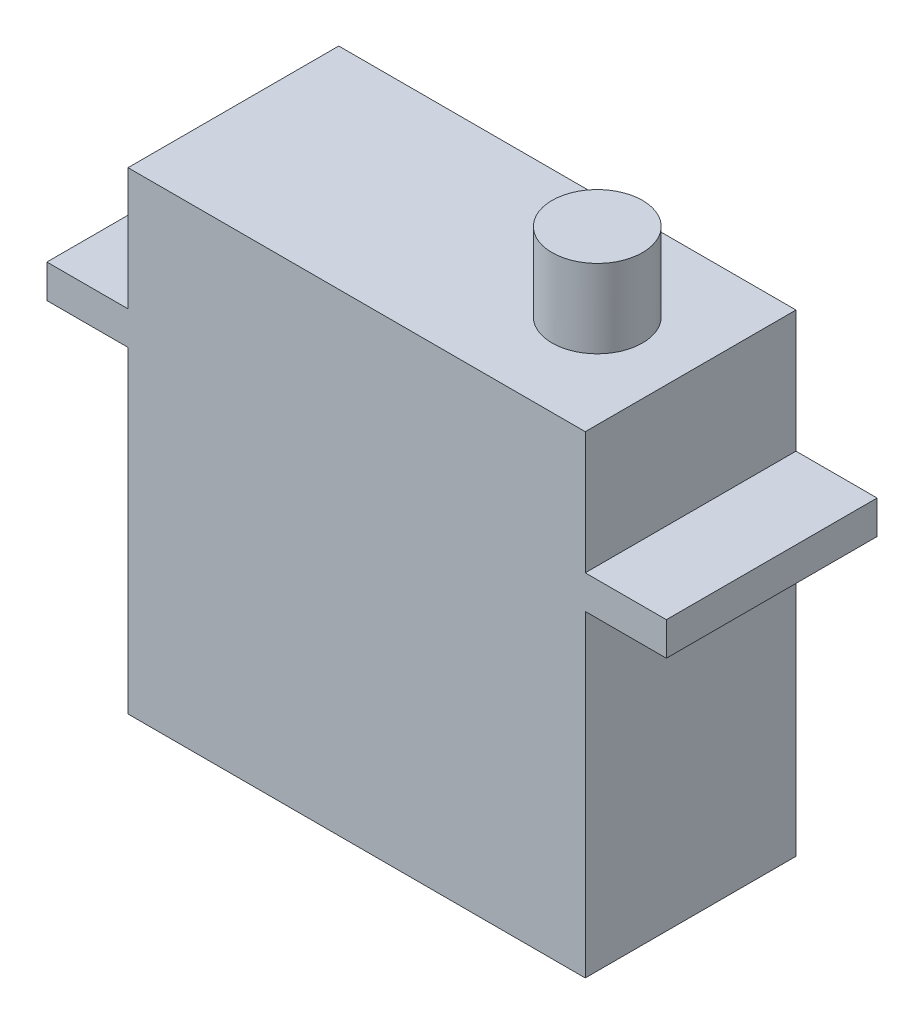
SolidWorks part; units mm, degrees
ref_plane "Front Plane" through (0, 0, 0) normal (0, 0, 1) x (1, 0, 0)
ref_plane "Top Plane" through (0, 0, 0) normal (0, 1, 0) x (1, 0, 0)
ref_plane "Right Plane" through (0, 0, 0) normal (1, 0, 0) x (0, 0, -1)
sketch "Sketch1" plane through (0, 0, 0) normal (0, 0, 1) x (1, 0, 0)
  line L1 (-14.605, 15.113) -> (14.605, 15.113)
  line L2 (-14.605, 15.113) -> (-14.605, -15.113)
  line L3 (-14.605, -15.113) -> (14.605, -15.113)
  line L4 (14.605, 15.113) -> (14.605, -15.113)
  line L5 (-14.605, 15.113) -> (14.605, -15.113) construction
  line L6 (-14.605, -15.113) -> (14.605, 15.113) construction
  point P0 (0, 0)
  dimension "D1" = 29.21
  dimension "D2" = 30.226
extrude "Boss-Extrude1" add sketch "Sketch1" along normal mid plane 13.462
sketch "Sketch2" plane through (0, 0, 6.731) normal (0, 0, 1) x (1, 0, 0)
  line L0 (-14.605, 15.113) -> (-14.605, -15.113) construction
  line L1 (-14.605, 7.3025) -> (-19.7866, 7.3025)
  line L2 (-14.605, 7.3025) -> (-14.605, 5.1689)
  line L3 (-14.605, 5.1689) -> (-19.7866, 5.1689)
  line L4 (-19.7866, 7.3025) -> (-19.7866, 5.1689)
  line L5 (-14.605, -15.113) -> (14.605, -15.113) construction
  line L6 (0, 0.5351) -> (0, -2.0067) construction
  dimension "D1" = 20.2819
  dimension "D2" = 2.1336
  dimension "D3" = 39.5732
extrude "Boss-Extrude2" add sketch "Sketch2" against normal up to surface (13.462 mm away) contours L1 L4 L3 L2 up to face at (0, 0, -6.731)
mirror "Mirror1" about plane through (0, 0, 0) normal (1, 0, 0) of "Boss-Extrude2"
sketch "Sketch3" plane through (0, 15.113, 0) normal (0, 1, 0) x (1, 0, 0)
  line L0 (14.605, -6.731) -> (14.605, 6.731) construction
  circle A0 centre (8.6423, 0) radius 2.8893
  dimension "D1" = 5.7785
  dimension "D2" = 3.0734
extrude "Boss-Extrude3" add sketch "Sketch3" along normal blind 5.0038
